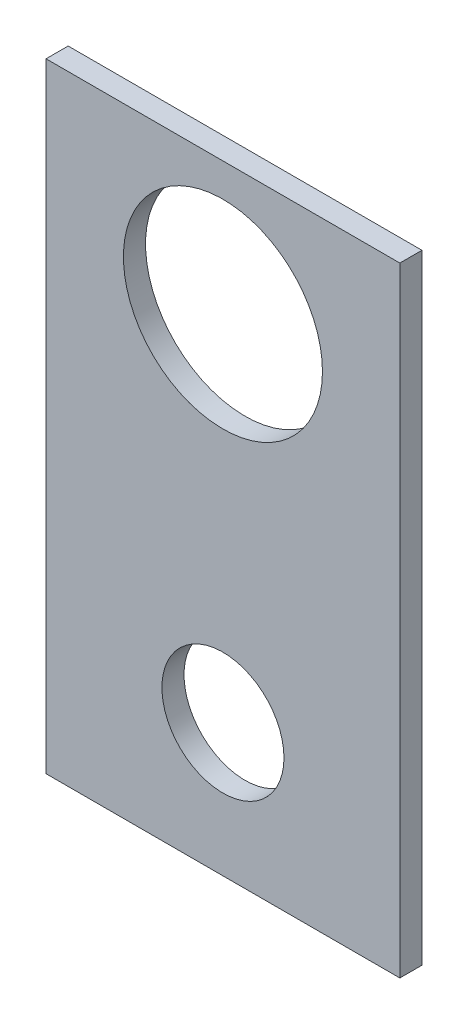
SolidWorks part; units mm, degrees
ref_plane "Front Plane" through (0, 0, 0) normal (0, 0, 1) x (1, 0, 0)
ref_plane "Top Plane" through (0, 0, 0) normal (0, 1, 0) x (1, 0, 0)
ref_plane "Right Plane" through (0, 0, 0) normal (1, 0, 0) x (0, 0, -1)
sketch "Sketch1" plane through (0, 0, 0) normal (0, 0, 1) x (1, 0, 0)
  line L1 (0, 0) -> (50.8, 0)
  line L2 (0, 0) -> (0, 88.9)
  line L3 (0, 88.9) -> (50.8, 88.9)
  line L4 (50.8, 0) -> (50.8, 88.9)
  circle A0 centre (25.4, 69.85) radius 14.2875
  circle A1 centre (25.4, 19.05) radius 8.763
  dimension "D3" = 28.575
  dimension "D4" = 17.526
  dimension "D1" = 88.9
  dimension "D2" = 50.8
  dimension "D5" = 50.8
  dimension "D6" = 19.05
  dimension "D7" = 19.05
  dimension "D8" = 25.4
extrude "Boss-Extrude1" add sketch "Sketch1" along normal blind 3.175
